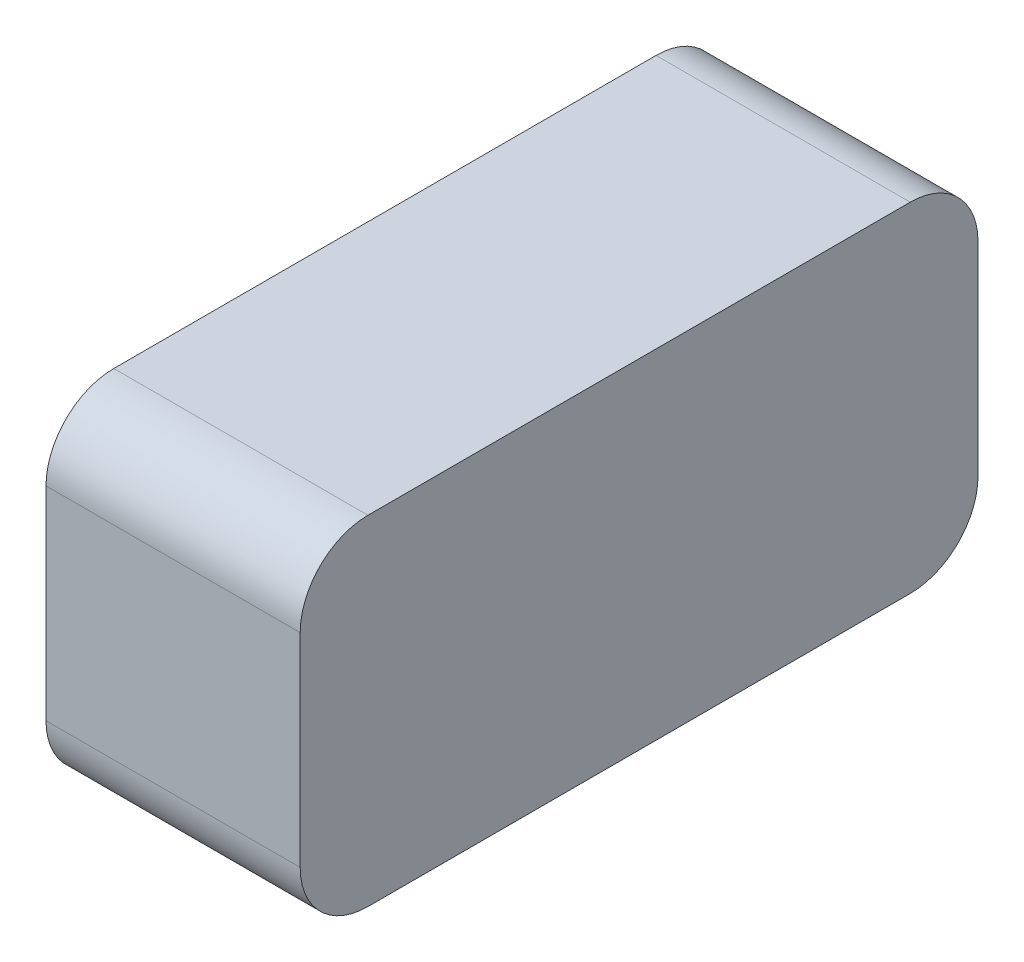
SolidWorks part; units mm, degrees
ref_plane "Front Plane" through (0, 0, 0) normal (0, 0, 1) x (1, 0, 0)
ref_plane "Top Plane" through (0, 0, 0) normal (0, 1, 0) x (1, 0, 0)
ref_plane "Right Plane" through (0, 0, 0) normal (1, 0, 0) x (0, 0, -1)
sketch "Sketch1" plane through (0, 0, 0) normal (1, 0, 0) x (0, 0, -1)
  line L1 (-40, 20) -> (40, 20)
  line L2 (-40, 20) -> (-40, -20)
  line L3 (-40, -20) -> (40, -20)
  line L4 (40, 20) -> (40, -20)
  line L5 (-40, 20) -> (40, -20) construction
  line L6 (-40, -20) -> (40, 20) construction
  point P0 (0, 0)
  dimension "D1" = 80
  dimension "D2" = 40
extrude "Boss-Extrude1" add sketch "Sketch1" along normal mid plane 30
fillet "Fillet1" radius 8 4 edges at (0, -20, -40) (0, -20, 40) (0, 20, -40) (0, 20, 40)
sketch "Sketch2" plane through (-15, 0, 0) normal (-1, 0, 0) x (0, 0, 1)
  circle A0 centre (0, 0) radius 10
  dimension "D1" = 20
extrude "Boss-Extrude2" add sketch "Sketch2" along normal blind 5
fillet "Fillet2" radius 3 1 edges at (-15, 0, 10)
